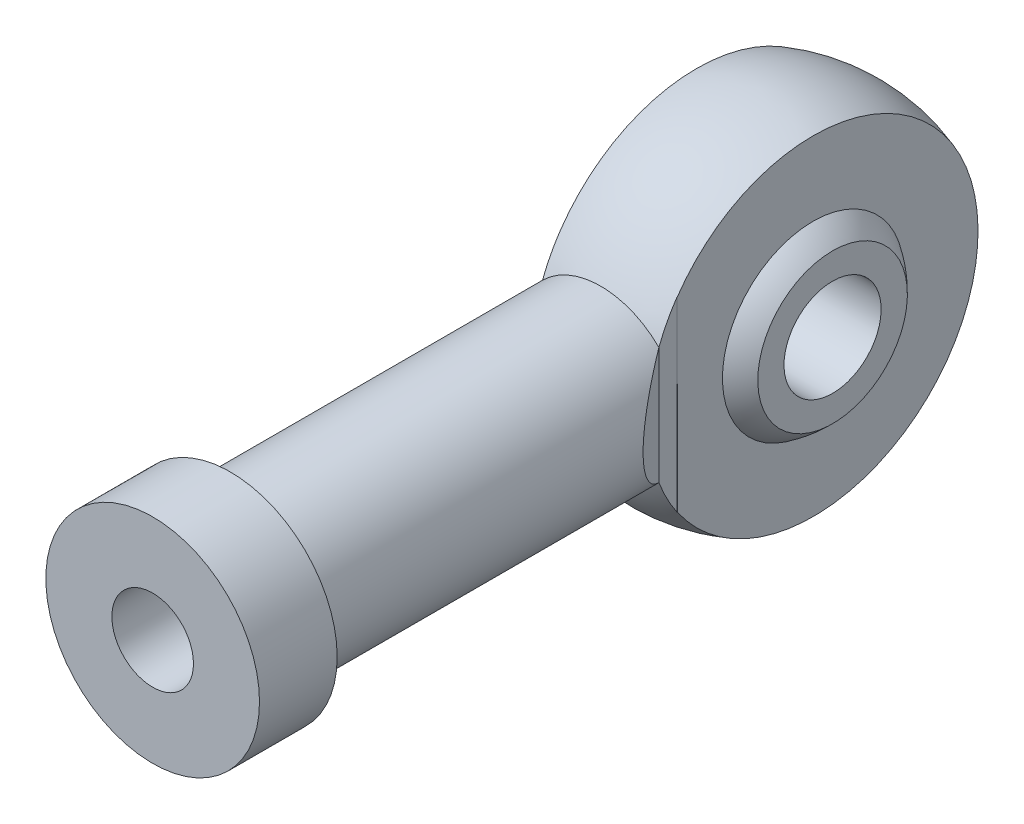
SolidWorks part; units mm, degrees
ref_plane "前视" through (0, 0, 0) normal (0, 0, 1) x (1, 0, 0)
ref_plane "上视" through (0, 0, 0) normal (0, 1, 0) x (1, 0, 0)
ref_plane "右视" through (0, 0, 0) normal (1, 0, 0) x (0, 0, -1)
sketch "草图1" plane through (0, 0, 0) normal (0, 0, 1) x (1, 0, 0)
  line L0 (0, 9) -> (0, 0) construction
  line L1 (-4, 3.8546) -> (-4, 2.4956)
  line L2 (4, 3.8546) -> (4, 2.5044)
  line L6 (-3, 8.4853) -> (-3, 4.6753)
  line L7 (3, 8.4853) -> (3, 4.6753)
  line L8 (-4, 13.1572) -> (-4, -15.5904) construction
  line L9 (-3, 13.1572) -> (-3, -15.5904) construction
  line L10 (0, 13.1572) -> (0, -15.5904) construction
  line L11 (3, 13.1572) -> (3, -15.5904) construction
  line L12 (4, 13.1572) -> (4, -15.5904) construction
  line L17 (4, 2.5044) -> (-4, 2.4956)
  line L18 (4, 0.0044) -> (-12.5958, -0.0139) construction
  arc A2 (3, 8.4853) -> (-3, 8.4853) centre (0, 0) ccw
  arc A3 (4, 3.8546) -> (3, 4.6753) centre (0, 0) ccw
  arc A4 (-3, 4.6753) -> (-4, 3.8546) centre (0, 0) ccw
  dimension "D1" = 2.5
  dimension "D4" = 9
  dimension "D5" = 5.555
  dimension "D2" = 4
  dimension "D3" = 4
  dimension "D7" = 3
  dimension "D8" = 3
revolve "旋转1" add sketch "草图1" angle 360 about L18
ref_plane "基准面1" through (0, 0, 27) normal (0, 0, 1) x (1, 0, 0)
sketch "草图3" plane through (0, 0, 27) normal (0, 0, 1) x (1, 0, 0)
  circle A0 centre (0, 0) radius 5.5
  dimension "D1" = 11
extrude "凸台-拉伸2" add sketch "草图3" along normal blind 4 separate body
sketch "草图4" plane through (0, 0, 27) normal (0, 0, -1) x (-1, 0, 0)
  circle A0 centre (0, 0) radius 4.25
  dimension "D1" = 8.5
extrude "凸台-拉伸3" add sketch "草图4" along normal blind 20
sketch "草图5" plane through (0, 0, 0) normal (0, 1, 0) x (1, 0, 0)
  line L0 (-2.9949, -7) -> (-2.9949, -7.9333)
  line L1 (-2.9949, -7.9333) -> (-4.25, -10)
  line L2 (-4.25, -7) -> (-4.25, -27) construction
  line L3 (-4.25, -10) -> (-4.25, -7)
  line L4 (-4.25, -7) -> (-2.9949, -7)
  line L5 (-2.994, -7.9333) -> (3.006, -7.9333) construction
  line L6 (0, -7) -> (0, -11.4226) construction
  line L7 (4.25, -7) -> (2.9949, -7)
  line L8 (4.25, -10) -> (4.25, -7)
  line L9 (2.9949, -7.9333) -> (4.25, -10)
  line L10 (2.9949, -7) -> (2.9949, -7.9333)
  dimension "D1" = 3
extrude "切除-拉伸1" cut sketch "草图5" against normal mid plane 20
hole_wizard "M5 螺纹孔1" positions "草图7" profile "草图6" tap size "M5" standard "GB"
sketch "草图7" plane through (0, 0, 31) normal (0, 0, 1) x (1, 0, 0)
  point P0 (0, 0)
sketch "草图6" plane through (0, 0, 31) normal (1, 0, 0) x (0, -1, 0)
  line L0 (0, 0) -> (0, 13.6618)
  line L1 (0, 13.6618) -> (2.1, 12.4)
  line L2 (2.1, 12.4) -> (2.1, 0)
  line L5 (2.1, 0) -> (0, 0)
  line L10 (0, 13.6618) -> (-2.1, 12.4) construction
  line L11 (0, -6.35) -> (0, 107.95) construction
  dimension "螺纹孔钻头直径" = 4.2
  dimension "螺纹孔钻头深度" = 12.4
  dimension "导头角度" = 118
cosmetic thread "孔螺蚊线1" parameters "D1"=10, "D2"=5
